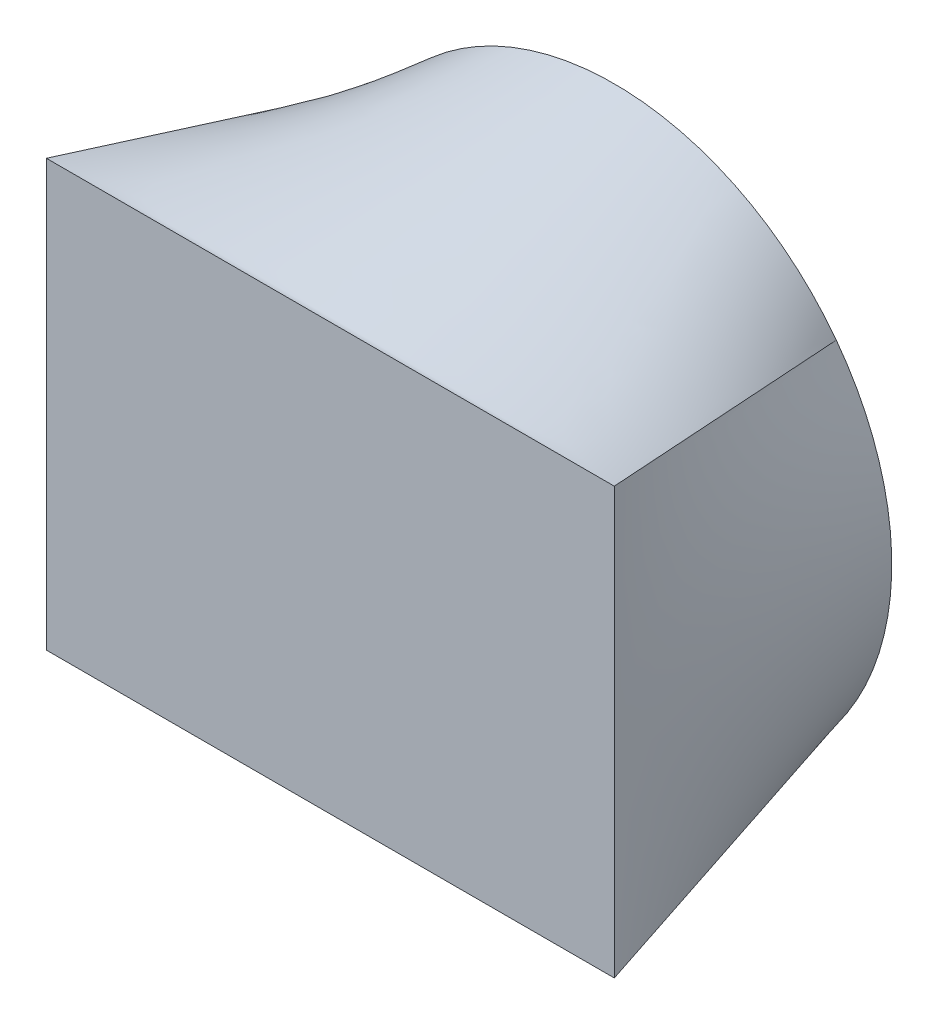
SolidWorks part; units mm, degrees
ref_plane "Ebene vorne" through (0, 0, 0) normal (0, 0, 1) x (1, 0, 0)
ref_plane "Ebene oben" through (0, 0, 0) normal (0, 1, 0) x (1, 0, 0)
ref_plane "Ebene rechts" through (0, 0, 0) normal (1, 0, 0) x (0, 0, -1)
sketch "Rechteck" plane through (0, 0, 0) normal (0, 0, 1) x (1, 0, 0)
  line L1 (0, 0) -> (100, 0)
  line L2 (0, 0) -> (0, 75)
  line L3 (0, 75) -> (100, 75)
  line L4 (100, 0) -> (100, 75)
  dimension "B" = 100
  dimension "H" = 75
ref_plane "Ebene1" through (0, 0, -50) normal (0, 0, 1) x (1, 0, 0)
sketch "Skizze2" plane through (0, 0, -50) normal (0, 0, 1) x (1, 0, 0)
  line L0 (50, 37.5) -> (50, 0) construction
  line L1 (50, 37.5) -> (0, 37.5) construction
  line L2 (0, 0) -> (0, 75) construction
  line L3 (0, 0) -> (100, 0) construction
  circle A0 centre (50, 37.5) radius 48.8603
  dimension "D" = 97.7205
loft "Ausformung1" add profiles "Rechteck", "Skizze2"
equation "\"FRechteck\"= \"B@Rechteck\" * \"H@Rechteck\""
equation "\"D@Skizze2\"=  sqr(\"FRechteck\" * 4 /  pi )"
